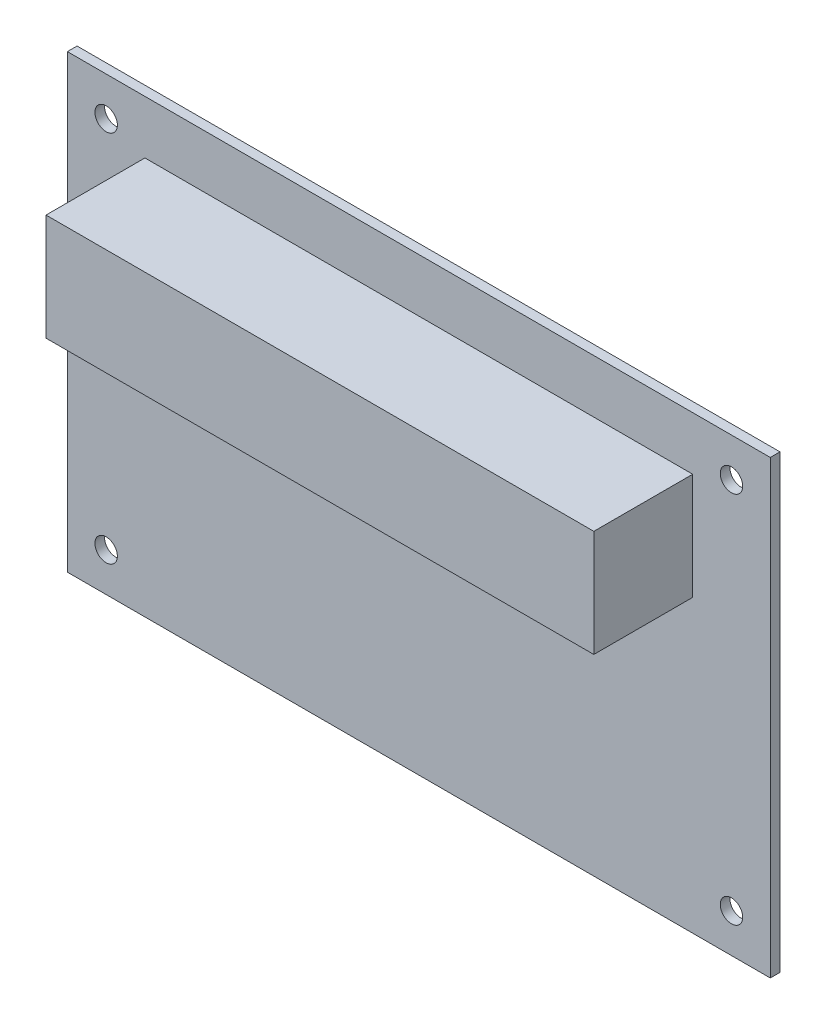
SolidWorks part; units mm, degrees
ref_plane "Plan de face" through (0, 0, 0) normal (0, 0, 1) x (1, 0, 0)
ref_plane "Plan de dessus" through (0, 0, 0) normal (0, 1, 0) x (1, 0, 0)
ref_plane "Plan de droite" through (0, 0, 0) normal (1, 0, 0) x (0, 0, -1)
sketch "Esquisse1" plane through (-4.2722, 0, 0) normal (0, 0, 1) x (1, 0, 0)
  line L1 (0, 0) -> (72.5, 0)
  line L2 (0, 0) -> (0, 46.5)
  line L3 (0, 46.5) -> (72.5, 46.5)
  line L4 (72.5, 0) -> (72.5, 46.5)
  circle A0 centre (4, 42.5) radius 1.16
  circle A1 centre (68.5, 42.5) radius 1.16
  circle A2 centre (68.5, 4) radius 1.16
  circle A3 centre (4, 4) radius 1.16
  point P9 (0, 0)
  point P10 (0, 0)
  point P13 (0, 0)
  point P16 (70.2267, 2.0082)
  point P17 (0, 0)
  dimension "D1" = 72.5
  dimension "D3" = 4
  dimension "D2" = 46.5
  dimension "D4" = 4
  dimension "D5" = 4
  dimension "D6" = 4
extrude "Boss.-Extru.1" add sketch "Esquisse1" along normal blind 1
sketch "Esquisse2" plane through (-4.2722, 0, 1) normal (0, 0, 1) x (1, 0, 0)
  line L0 (72.5, 46.5) -> (0, 46.5) construction
  line L1 (8, 41) -> (64.5, 41)
  line L2 (8, 41) -> (8, 30)
  line L3 (8, 30) -> (64.5, 30)
  line L4 (64.5, 41) -> (64.5, 30)
  line L5 (0, 46.5) -> (0, 0) construction
  line L6 (72.5, 0) -> (72.5, 46.5) construction
  dimension "D1" = 5.5
  dimension "D2" = 11
  dimension "D3" = 56.5
  dimension "D4" = 8
  dimension "D5" = 8
extrude "Boss.-Extru.3" add sketch "Esquisse2" along normal blind 10.2
